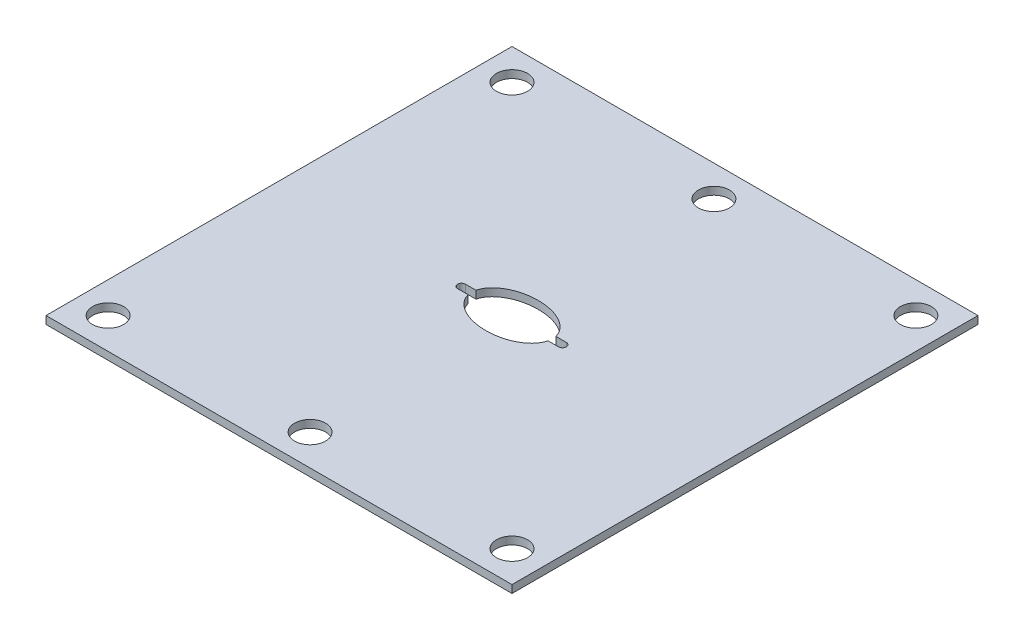
SolidWorks part; units mm, degrees
ref_plane "Front Plane" through (0, 0, 0) normal (0, 0, 1) x (1, 0, 0)
ref_plane "Top Plane" through (0, 0, 0) normal (0, 1, 0) x (1, 0, 0)
ref_plane "Right Plane" through (0, 0, 0) normal (1, 0, 0) x (0, 0, -1)
sketch "Sketch1" plane through (0, 0, 0) normal (0, 1, 0) x (1, 0, 0)
  line L1 (30, -30) -> (-30, -30)
  line L2 (30, -30) -> (30, 30)
  line L3 (30, 30) -> (-30, 30)
  line L4 (-30, -30) -> (-30, 30)
  line L5 (30, -30) -> (-30, 30) construction
  line L6 (30, 30) -> (-30, -30) construction
  point P0 (0, 0)
  dimension "D1" = 60
  dimension "D2" = 60
extrude "Boss-Extrude1" add sketch "Sketch1" along normal blind 1
hole_wizard "Ø4.0 (4) Diameter Hole1" positions "Sketch13" profile "Sketch12" hole size "Ø4.0" standard "ANSI Metric" end condition up to next
sketch "Sketch13" plane through (0, 1, 0) normal (0, 1, 0) x (1, 0, 0)
  line L0 (0, 30) -> (0, -30) construction
  line L1 (30, 30) -> (-30, 30) construction
  line L2 (-30, -30) -> (30, -30) construction
  line L4 (-30, 0) -> (30, 0) construction
  line L5 (-30, 30) -> (-30, -30) construction
  line L6 (30, -30) -> (30, 30) construction
  point P17 (26, 26)
  point P24 (0, 26)
  point P27 (-26, 26)
  point P28 (0, -26)
  point P29 (26, -26)
  point P30 (-26, -26)
  dimension "D1" = 4
  dimension "D2" = 4
sketch "Sketch12" plane through (26, 1, -26) normal (1, 0, 0) x (0, 0, 1)
  line L0 (0, 0) -> (0, 1)
  line L1 (0, 1) -> (2, 1)
  line L2 (2, 1) -> (2, 0)
  line L5 (2, 0) -> (0, 0)
  line L11 (0, -6.35) -> (0, 107.95) construction
  dimension "Thru Hole Dia." = 4
  dimension "Thru Hole Depth" = 1
sketch "Sketch3" plane through (0, 1, 0) normal (0, 1, 0) x (1, 0, 0)
  circle A0 centre (6.5, 0) radius 0.5
  circle A1 centre (-6.5, 0) radius 0.5
  dimension "D1" = 1
  dimension "D2" = 1
  dimension "D3" = 13
  dimension "D4" = 6.5
extrude "Cut-Extrude1" cut sketch "Sketch3" against normal blind 5
sketch "Sketch9" plane through (0, 1, 0) normal (0, 1, 0) x (1, 0, 0)
  line L1 (6.5, -0.5) -> (-6.5, -0.5)
  line L2 (6.5, -0.5) -> (6.5, 0.5)
  line L3 (6.5, 0.5) -> (-6.5, 0.5)
  line L4 (-6.5, -0.5) -> (-6.5, 0.5)
  line L5 (6.5, -0.5) -> (-6.5, 0.5) construction
  line L6 (6.5, 0.5) -> (-6.5, -0.5) construction
  circle A0 centre (-6.5, 0) radius 0.5 construction
  point P0 (0, 0)
  dimension "D1" = 13
extrude "Cut-Extrude7" cut sketch "Sketch9" against normal blind 5
sketch "Sketch10" plane through (0, 1, 0) normal (0, 1, 0) x (1, 0, 0)
  ellipse E0 centre (0, 0) end of major axis (-5.1936, 0) minor radius 3.3692
extrude "Cut-Extrude8" cut sketch "Sketch10" against normal blind 5
